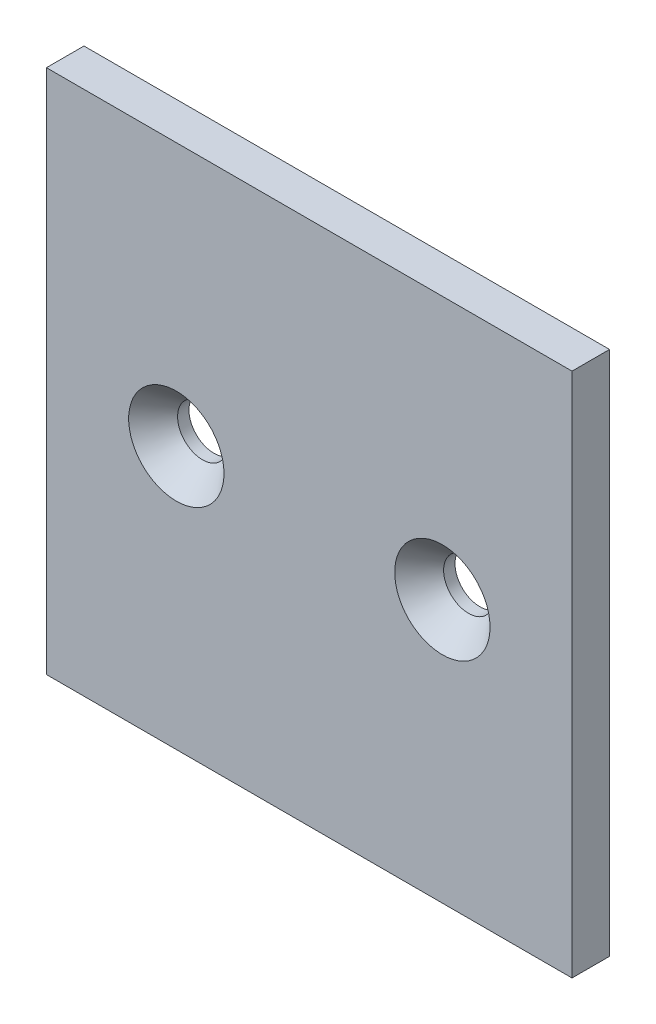
SolidWorks part; units mm, degrees
ref_plane "Front Plane" through (0, 0, 0) normal (0, 0, 1) x (1, 0, 0)
ref_plane "Top Plane" through (0, 0, 0) normal (0, 1, 0) x (1, 0, 0)
ref_plane "Right Plane" through (0, 0, 0) normal (1, 0, 0) x (0, 0, -1)
sketch "Sketch1" plane through (0, 0, 0) normal (0, 0, 1) x (1, 0, 0)
  line L1 (-44.45, 44.45) -> (44.45, 44.45)
  line L2 (-44.45, 44.45) -> (-44.45, -44.45)
  line L3 (-44.45, -44.45) -> (44.45, -44.45)
  line L4 (44.45, 44.45) -> (44.45, -44.45)
  line L5 (-44.45, 44.45) -> (44.45, -44.45) construction
  line L6 (-44.45, -44.45) -> (44.45, 44.45) construction
  circle A0 centre (-22.479, 0) radius 4.191
  circle A1 centre (22.521, 0) radius 4.15
  point P0 (0, 0)
  dimension "D3" = 8.3
  dimension "D4" = 8.382
  dimension "D1" = 88.9
  dimension "D2" = 88.9
  dimension "D5" = 45
  dimension "D6" = 22.479
extrude "Boss-Extrude1" add sketch "Sketch1" against normal blind 6.35
hole_wizard "CSK for 5/16 Flat Head Machine Screw1" positions "3DSketch1" profile "Sketch2" countersink size "5/16" standard "ANSI Inch"
sketch3d "3DSketch1"
  line L0 (-22.479, 0, -6.35) -> (-22.479, 0, 0) construction
  line L1 (22.521, 0, -6.35) -> (22.521, 0, 0) construction
  circle A0 centre (-22.479, 0, 0) radius 4.191 construction
  point P0 (-20.1102, 3.4574, 0)
  point P4 (-22.479, 0, 4.191)
  point P5 (-22.479, 0, 0)
  point P9 (22.521, 0, 0)
sketch "Sketch2" plane through (-22.479, 0, 0) normal (1, 0, 0) x (0, -1, 0)
  line L0 (0, 0) -> (0, 35.2995)
  line L1 (0, 35.2995) -> (4.2164, 32.766)
  line L2 (4.2164, 32.766) -> (4.2164, 4.4267)
  line L3 (4.2164, 4.4267) -> (8.0645, 0)
  line L5 (8.0645, 0) -> (0, 0)
  line L6 (-4.2164, 4.4267) -> (-8.0645, 0) construction
  line L10 (0, 35.2995) -> (-4.2164, 32.766) construction
  line L11 (0, -6.35) -> (0, 107.95) construction
  dimension "Hole Dia." = 8.4328
  dimension "Hole Depth" = 32.766
  dimension "Near C'Sink Dia." = 16.129
  dimension "Near C'Sink Angle" = 82
  dimension "Drill Angle" = 118
